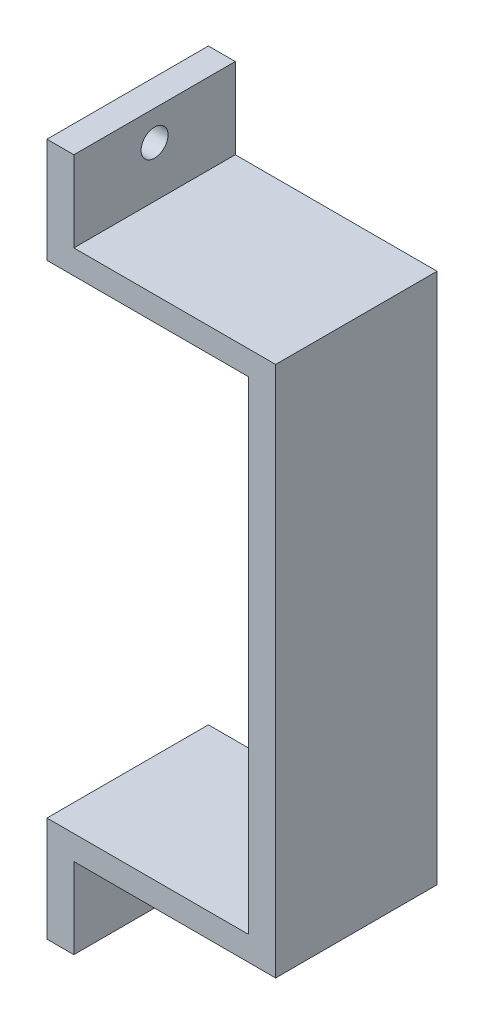
SolidWorks part; units mm, degrees
ref_plane "前视基准面" through (0, 0, 0) normal (0, 0, 1) x (1, 0, 0)
ref_plane "上视基准面" through (0, 0, 0) normal (0, 1, 0) x (1, 0, 0)
ref_plane "右视基准面" through (0, 0, 0) normal (1, 0, 0) x (0, 0, -1)
sketch "草图1" plane through (0, 0, 0) normal (0, 0, 1) x (1, 0, 0)
  line L0 (0, 25.75) -> (0, 17.95)
  line L1 (0, 25.75) -> (2, 25.75)
  line L2 (2, 25.75) -> (2, 19.75)
  line L3 (2, 19.75) -> (17, 19.75)
  line L4 (17, 19.75) -> (17, -19.75)
  line L5 (17, -19.75) -> (2, -19.75)
  line L6 (2, -19.75) -> (2, -25.75)
  line L7 (2, -25.75) -> (0, -25.75)
  line L8 (0, 17.95) -> (15, 17.95)
  line L9 (15, 17.95) -> (15, -17.95)
  line L10 (15, -17.95) -> (0, -17.95)
  line L11 (0, -17.95) -> (0, -25.75)
  dimension "D1" = 51.5
  dimension "D2" = 25.75
  dimension "D3" = 2
  dimension "D4" = 1.8
  dimension "D5" = 2
  dimension "D6" = 1.8
  dimension "D7" = 2
  dimension "D8" = 13
  dimension "D9" = 6
  dimension "D10" = 6
  dimension "D11" = 13
extrude "凸台-拉伸1" add sketch "草图1" along normal blind 12
sketch "草图2" plane through (0, 0, 0) normal (-1, 0, 0) x (0, 0, 1)
  line L0 (12, 25.75) -> (0, 25.75) construction
  line L1 (12, -25.75) -> (0, -25.75) construction
  line L2 (12, -17.95) -> (12, -25.75) construction
  line L3 (12, 25.75) -> (12, 17.95) construction
  circle A0 centre (6, 23.5311) radius 1
  circle A1 centre (6, -22.75) radius 1
  dimension "D1" = 2
  dimension "D2" = 2
  dimension "D3" = 2.2189
  dimension "D4" = 3
  dimension "D5" = 6
  dimension "D6" = 6
extrude "切除-拉伸1" cut sketch "草图2" against normal blind 3
